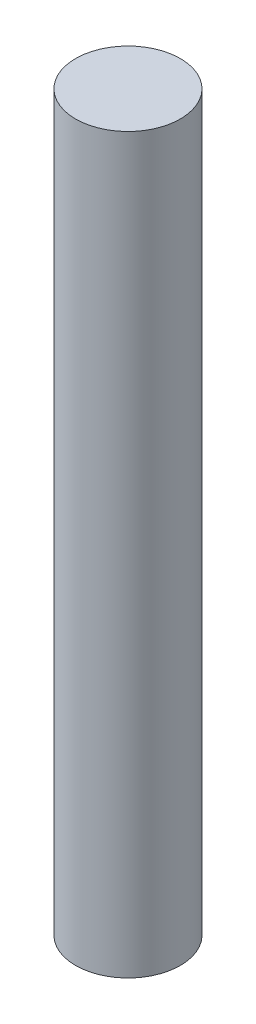
SolidWorks part; units mm, degrees
ref_plane "Plan de face" through (0, 0, 0) normal (0, 0, 1) x (1, 0, 0)
ref_plane "Plan de dessus" through (0, 0, 0) normal (0, 1, 0) x (1, 0, 0)
ref_plane "Plan de droite" through (0, 0, 0) normal (1, 0, 0) x (0, 0, -1)
sketch "Esquisse1" plane through (0, 0, 0) normal (0, 1, 0) x (1, 0, 0)
  circle A0 centre (0, 0) radius 1
extrude "Extrusion1" add sketch "Esquisse1" along normal blind 14
